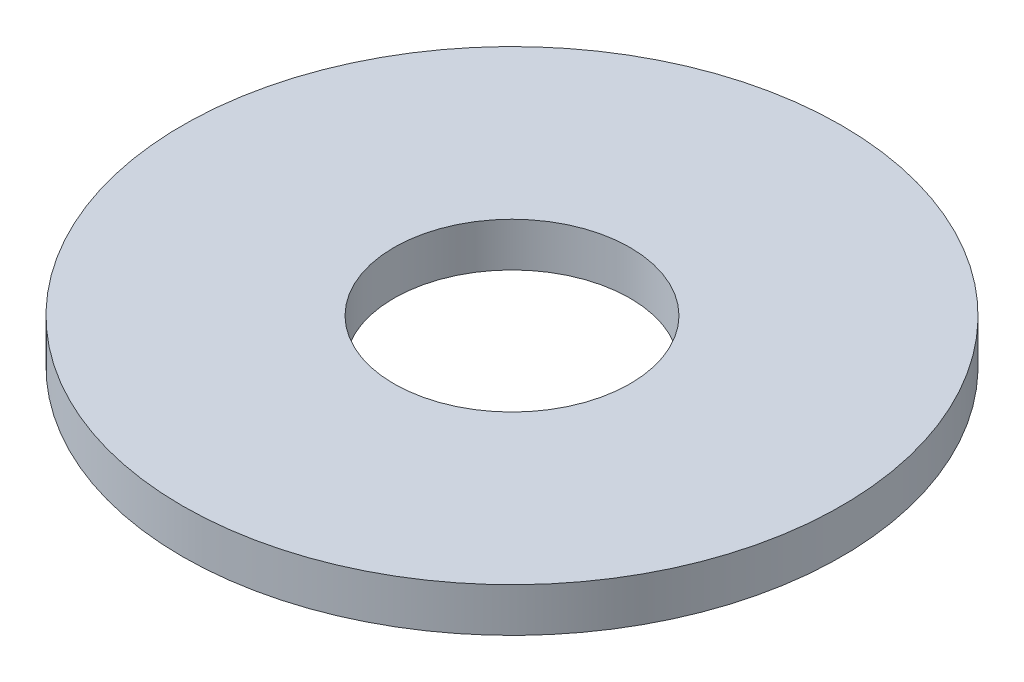
SolidWorks part; units mm, degrees
ref_plane "Piano frontale" through (0, 0, 0) normal (0, 0, 1) x (1, 0, 0)
ref_plane "Piano superiore" through (0, 0, 0) normal (0, 1, 0) x (1, 0, 0)
ref_plane "Piano destro" through (0, 0, 0) normal (1, 0, 0) x (0, 0, -1)
sketch "Schizzo1" plane through (0, 0, 0) normal (0, 1, 0) x (1, 0, 0)
  circle A0 centre (0, 0) radius 2.15
  circle A1 centre (0, 0) radius 6
extrude "Estrusione-Estrusione1" add sketch "Schizzo1" along normal blind 0.8
scale "Scale1" scale about centroid uniform scaling yes scale factor 1.76744
